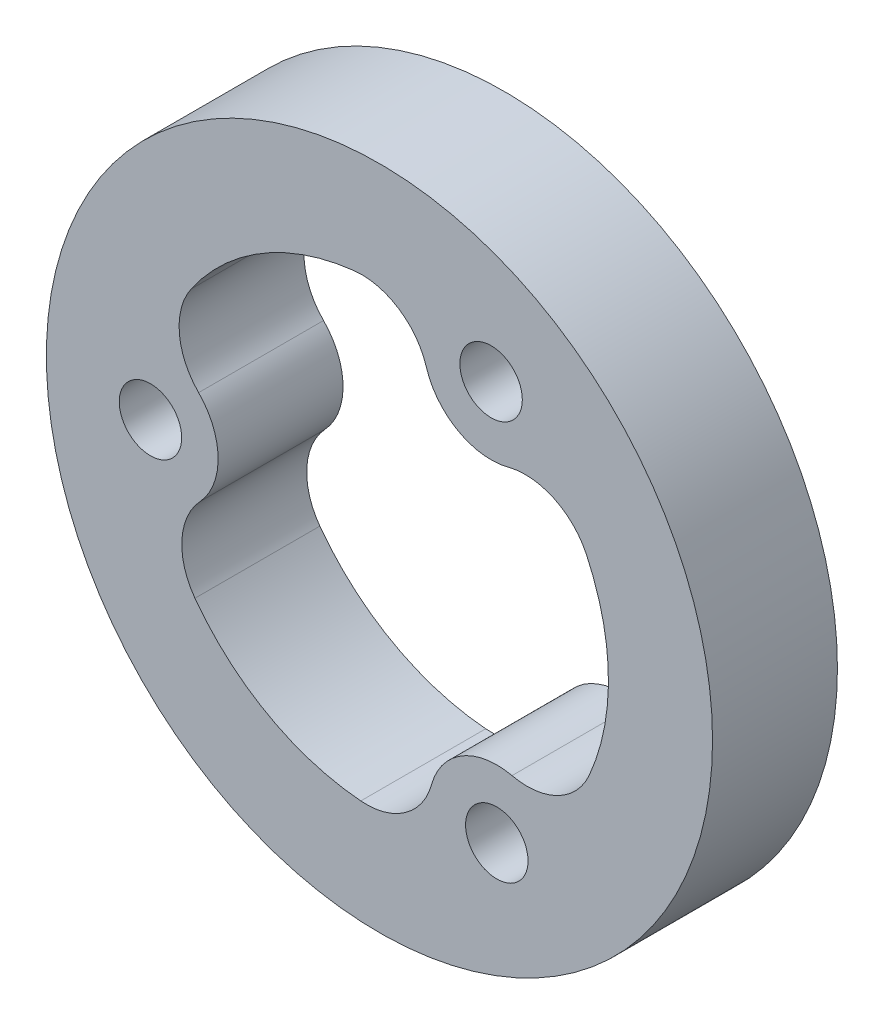
SolidWorks part; units mm, degrees
ref_plane "Plan de face" through (0, 0, 0) normal (0, 0, 1) x (1, 0, 0)
ref_plane "Plan de dessus" through (0, 0, 0) normal (0, 1, 0) x (1, 0, 0)
ref_plane "Plan de droite" through (0, 0, 0) normal (1, 0, 0) x (0, 0, -1)
sketch "Esquisse1" plane through (0, 0, 0) normal (0, 0, 1) x (1, 0, 0)
  line L0 (5.3623, 9.6045) -> (0, 0) construction
  line L1 (-10.9989, -0.1583) -> (5.3623, 9.6045) construction
  line L2 (5.3623, 9.6045) -> (5.6365, -9.4461) construction
  line L3 (5.6365, -9.4461) -> (-10.9989, -0.1583) construction
  circle A0 centre (0, 0) radius 16
  arc A2 (-8.6215, -2.3744) -> (-8.6863, 2.1252) centre (-10.9989, -0.1583) ccw
  circle A3 centre (-10.9989, -0.1583) radius 1.5
  arc A4 (-8.6215, -2.3744) -> (-8.8628, -6.5154) centre (-6.2442, -4.5904) ccw
  arc A5 (-9.0466, 6.2577) -> (-8.6863, 2.1252) centre (-6.3738, 4.4088) ccw
  arc A6 (-8.8628, -6.5154) -> (-0.896, -10.9635) centre (0, 0) ccw
  circle A7 centre (-10.9989, -0.1583) radius 3.25 construction
  circle A8 centre (5.3623, 9.6045) radius 3.25 construction
  circle A9 centre (5.3623, 9.6045) radius 1.5
  arc A10 (9.9426, 4.7058) -> (6.1837, 6.4599) centre (7.005, 3.3154) ccw
  arc A11 (2.2545, 8.6537) -> (6.1837, 6.4599) centre (5.3623, 9.6045) ccw
  arc A12 (2.2545, 8.6537) -> (-1.2111, 10.9331) centre (-0.8533, 7.7029) ccw
  circle A13 centre (5.6365, -9.4461) radius 3.25 construction
  circle A14 centre (5.6365, -9.4461) radius 1.5
  arc A15 (-0.896, -10.9635) -> (2.5026, -8.5852) centre (-0.6312, -7.7242) ccw
  arc A16 (6.367, -6.2793) -> (2.5026, -8.5852) centre (5.6365, -9.4461) ccw
  arc A17 (6.367, -6.2793) -> (10.0739, -4.4177) centre (7.0975, -3.1125) ccw
  arc A18 (10.0739, -4.4177) -> (9.9426, 4.7058) centre (0, 0) ccw
  circle A19 centre (0, 0) radius 7.75 construction
  arc A20 (-1.2111, 10.9331) -> (-9.0466, 6.2577) centre (0, 0) ccw
  circle A21 centre (0, 0) radius 9 construction
  point P32 (0, 0)
  dimension "D1" = 32
  dimension "D2" = 6.5
  dimension "D3" = 3
  dimension "D4" = 3
  dimension "D5" = 15.5
  dimension "D7" = 18
  dimension "D9" = 11
  dimension "D10" = 3.25
  dimension "D11" = 3.25
  dimension "D12" = 7.75
  dimension "D6" = 11
  dimension "D8" = 19.0506
  dimension "D13" = 7.75
extrude "Boss.-Extru.1" add sketch "Esquisse1" along normal blind 6
